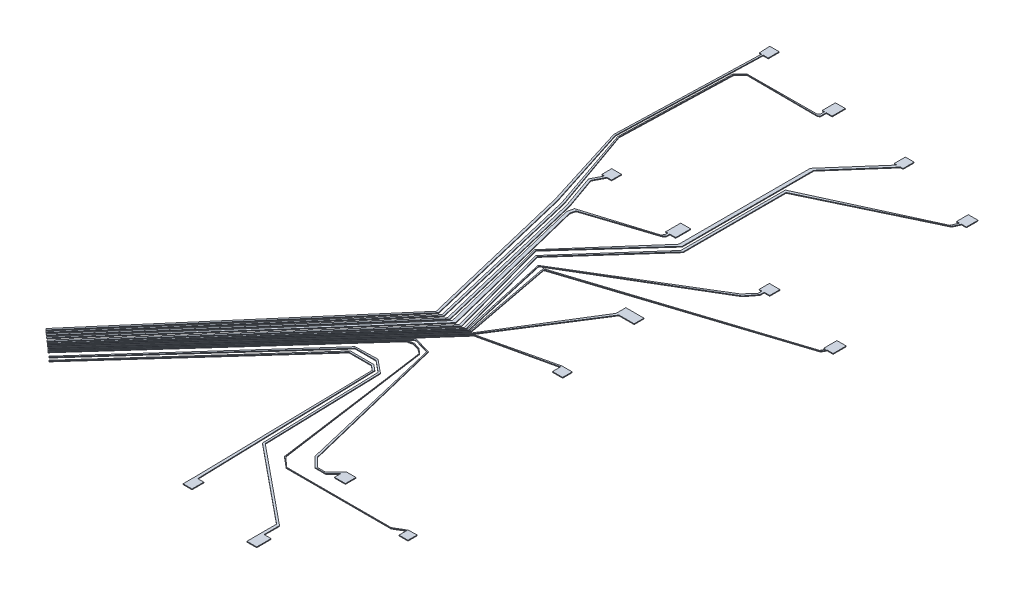
SolidWorks part; units mm, degrees
ref_plane "Front Plane" through (0, 0, 0) normal (0, 0, 1) x (1, 0, 0)
ref_plane "Top Plane" through (0, 0, 0) normal (0, 1, 0) x (1, 0, 0)
ref_plane "Right Plane" through (0, 0, 0) normal (1, 0, 0) x (0, 0, -1)
sketch "Sketch3" plane through (0, 0, 0) normal (0, 1, 0) x (1, 0, 0)
  line L0 (-35.1041, -266.8621) -> (862.8959, -266.8621) construction
  line L1 (-38.0962, 94.7327) -> (-39.2981, 55.2572)
  line L2 (-39.2981, 55.2572) -> (-31.9561, 31.8665)
  line L3 (-31.9561, 31.8665) -> (-21.5828, -11.2878)
  line L4 (-21.5828, -11.2878) -> (-71.1597, -69.0968)
  line L5 (-71.1597, -69.0968) -> (-70.7842, -69.4189)
  line L6 (-70.7842, -69.4189) -> (-20.9311, -11.2878)
  line L7 (-20.9311, -11.2878) -> (-31.3218, 31.8665)
  line L8 (-31.3218, 31.8665) -> (-38.8599, 55.2572)
  line L9 (-38.8599, 55.2572) -> (-37.658, 94.7327)
  line L10 (-37.658, 94.7327) -> (-36.253, 94.7327)
  line L11 (-36.253, 94.7327) -> (-36.253, 97.745)
  line L12 (-36.253, 97.745) -> (-38.8599, 97.745)
  line L13 (-38.8599, 97.745) -> (-38.6971, 94.7327)
  line L14 (-38.6971, 94.7327) -> (-38.0962, 94.7327)
  line L15 (-15.7108, 89.6823) -> (-15.7108, 88.591)
  line L17 (-35.4155, 88.0044) -> (-37.2858, 86.1341)
  line L18 (-37.2858, 86.1341) -> (-38.2259, 55.2572)
  line L19 (-38.2259, 55.2572) -> (-30.2079, 31.8665)
  line L20 (-30.2079, 31.8665) -> (-19.9928, -11.2878)
  line L21 (-19.9928, -11.2878) -> (-70.5361, -69.6927)
  line L22 (-70.5361, -69.6927) -> (-70.2221, -69.9644)
  line L23 (-70.2221, -69.9644) -> (-19.4438, -11.2878)
  line L24 (-19.4438, -11.2878) -> (-29.7, 32.0406)
  line L25 (-29.7, 32.0406) -> (-37.9562, 55.3497)
  line L26 (-37.9562, 55.3497) -> (-37.0216, 86.0456)
  line L27 (-37.0216, 86.0456) -> (-35.2614, 87.8504)
  line L28 (-35.2614, 87.8504) -> (-15.7108, 87.7531)
  line L29 (-15.7108, 87.7531) -> (-15.2357, 88.1064)
  line L30 (-15.2357, 88.1064) -> (-15.2357, 89.6823)
  line L31 (-15.2357, 89.6823) -> (-13.6188, 89.6823)
  line L32 (-13.6188, 89.6823) -> (-13.6188, 93.3116)
  line L33 (-13.6188, 93.3116) -> (-16.325, 93.3116)
  line L34 (-16.325, 93.3116) -> (-16.325, 89.6823)
  line L35 (-16.325, 89.6823) -> (-15.7108, 89.6823)
  line L36 (-15.7108, 88.591) -> (-16.1954, 88.1064)
  line L37 (-16.1954, 88.1064) -> (-35.4155, 88.0044)
  line L38 (-30.6711, 44.1014) -> (-32.1687, 41.1714)
  line L39 (-32.1687, 41.1714) -> (-28.9456, 32.0406)
  line L40 (-28.9456, 32.0406) -> (-18.4952, -11.2878)
  line L41 (-18.4952, -11.2878) -> (-69.8872, -70.3011)
  line L42 (-69.8872, -70.3011) -> (-69.5247, -70.6168)
  line L43 (-69.5247, -70.6168) -> (-17.8577, -11.2878)
  line L44 (-17.8577, -11.2878) -> (-28.3432, 32.1859)
  line L45 (-28.3432, 32.1859) -> (-31.515, 41.1714)
  line L46 (-31.515, 41.1714) -> (-30.0174, 44.1014)
  line L47 (-30.0174, 44.1014) -> (-28.7234, 44.1014)
  line L48 (-28.7234, 44.1014) -> (-28.7234, 46.8397)
  line L49 (-28.7234, 46.8397) -> (-31.4199, 46.8397)
  line L50 (-31.4199, 46.8397) -> (-31.4199, 44.1014)
  line L51 (-31.4199, 44.1014) -> (-30.6711, 44.1014)
  line L52 (-8.3665, 39.2375) -> (-8.3665, 38.4261)
  line L53 (-8.3665, 38.4261) -> (-8.9614, 37.743)
  line L54 (-8.9614, 37.743) -> (-27.0118, 32.1859)
  line L55 (-27.0118, 32.1859) -> (-27.41, 30.4396)
  line L56 (-27.41, 30.4396) -> (-17.1484, -11.2878)
  line L57 (-17.1484, -11.2878) -> (-69.1213, -70.9681)
  line L58 (-69.1213, -70.9681) -> (-68.8091, -71.24)
  line L59 (-68.8091, -71.24) -> (-16.1954, -11.2878)
  line L60 (-16.1954, -11.2878) -> (-26.6101, 30.4396)
  line L61 (-26.6101, 30.4396) -> (-26.2847, 31.8665)
  line L62 (-26.2847, 31.8665) -> (-8.3665, 37.743)
  line L63 (-8.3665, 37.743) -> (-7.8273, 38.3575)
  line L64 (-7.8273, 38.3575) -> (-7.8273, 39.2375)
  line L65 (-7.8273, 39.2375) -> (-6.2056, 39.2375)
  line L66 (-6.2056, 39.2375) -> (-6.2056, 43.3527)
  line L67 (-6.2056, 43.3527) -> (-8.9614, 43.3527)
  line L68 (-8.9614, 43.3527) -> (-8.9614, 39.2375)
  line L69 (-8.9614, 39.2375) -> (-8.3665, 39.2375)
  line L70 (6.9786, 86.9535) -> (-4.1836, 74.2344)
  line L71 (-4.1836, 74.2344) -> (-4.1836, 38.0503)
  line L72 (-4.1836, 38.0503) -> (-22.7104, 16.9395)
  line L73 (-22.7104, 16.9395) -> (-15.2357, -11.2878)
  line L74 (-15.2357, -11.2878) -> (-68.267, -71.7157)
  line L75 (-68.267, -71.7157) -> (-67.9028, -72.0353)
  line L76 (-67.9028, -72.0353) -> (-14.5911, -11.2878)
  line L77 (-14.5911, -11.2878) -> (-22.3907, 16.9395)
  line L78 (-22.3907, 16.9395) -> (-3.2205, 38.0503)
  line L79 (-3.2205, 38.0503) -> (-3.2205, 74.2344)
  line L80 (-3.2205, 74.2344) -> (7.9417, 86.9535)
  line L81 (7.9417, 86.9535) -> (8.6346, 86.9535)
  line L82 (8.6346, 86.9535) -> (8.6346, 90.0049)
  line L83 (8.6346, 90.0049) -> (6.2136, 90.0049)
  line L84 (6.2136, 90.0049) -> (6.2136, 86.9535)
  line L85 (6.2136, 86.9535) -> (6.9786, 86.9535)
  line L86 (29.4131, 81.7337) -> (28.6128, 81.7337)
  line L87 (28.6128, 81.7337) -> (28.6128, 84.935)
  line L88 (28.6128, 84.935) -> (31.2759, 84.935)
  line L89 (31.2759, 84.935) -> (31.2759, 81.7337)
  line L90 (31.2759, 81.7337) -> (29.9443, 81.7337)
  line L91 (29.4131, 81.7337) -> (28.6128, 79.8607)
  line L92 (28.6128, 79.8607) -> (-2.432, 65.6299)
  line L93 (-2.432, 65.6299) -> (-2.432, 36.8539)
  line L94 (-2.432, 36.8539) -> (-21.1993, 15.6499)
  line L95 (-21.1993, 15.6499) -> (-13.8535, -11.2878)
  line L96 (-13.8535, -11.2878) -> (-67.7398, -72.1703)
  line L97 (-67.7398, -72.1703) -> (-67.4613, -72.4168)
  line L98 (-67.4613, -72.4168) -> (-13.3568, -11.2878)
  line L99 (-13.3568, -11.2878) -> (-20.7026, 15.6499)
  line L100 (-20.7026, 15.6499) -> (-1.7624, 36.8539)
  line L101 (-1.7624, 36.8539) -> (-1.7624, 65.1584)
  line L102 (-1.7624, 65.1584) -> (29.1038, 79.8607)
  line L103 (29.1038, 79.8607) -> (29.9443, 81.7337)
  line L104 (18.4293, 38.3575) -> (18.4293, 37.2589)
  line L105 (18.4293, 37.2589) -> (16.0951, 34.6456)
  line L106 (16.0951, 34.6456) -> (-18.4952, 13.6781)
  line L107 (-18.4952, 13.6781) -> (-13.0522, -11.2878)
  line L108 (-13.0522, -11.2878) -> (-67.3236, -72.5386)
  line L109 (-67.3236, -72.5386) -> (-67.1813, -72.6647)
  line L110 (-67.1813, -72.6647) -> (-12.6528, -11.2878)
  line L111 (-12.6528, -11.2878) -> (-18.2652, 13.607)
  line L112 (-18.2652, 13.607) -> (16.8664, 34.4724)
  line L113 (16.8664, 34.4724) -> (19.0123, 37.2589)
  line L114 (19.0123, 37.2589) -> (19.0123, 38.3575)
  line L115 (19.0123, 38.3575) -> (20.5371, 38.3575)
  line L116 (20.5371, 38.3575) -> (20.5371, 41.1714)
  line L117 (20.5371, 41.1714) -> (17.6287, 41.1714)
  line L118 (17.6287, 41.1714) -> (17.6287, 38.3575)
  line L119 (17.6287, 38.3575) -> (18.4293, 38.3575)
  line L120 (41.0327, 33.2477) -> (40.5426, 32.1555)
  line L121 (40.5426, 32.1555) -> (-17.0297, 13.607)
  line L122 (-17.0297, 13.607) -> (-12.2554, -11.2878)
  line L123 (-12.2554, -11.2878) -> (-66.9593, -72.862)
  line L124 (-66.9593, -72.862) -> (-66.7471, -73.0505)
  line L125 (-66.7471, -73.0505) -> (-11.9371, -11.3568)
  line L126 (-11.9371, -11.3568) -> (-16.6818, 13.3837)
  line L127 (-16.6818, 13.3837) -> (40.7986, 32.0406)
  line L128 (40.7986, 32.0406) -> (41.4867, 33.2477)
  line L129 (41.4867, 33.2477) -> (43.0955, 33.2477)
  line L130 (43.0955, 33.2477) -> (43.0955, 36.8539)
  line L131 (43.0955, 36.8539) -> (40.5426, 36.8539)
  line L132 (40.5426, 36.8539) -> (40.5426, 33.2477)
  line L133 (40.5426, 33.2477) -> (41.0327, 33.2477)
  line L134 (3.6561, 15.6499) -> (3.6561, 12.9528)
  line L135 (3.6561, 12.9528) -> (-11.3992, -11.3568)
  line L136 (-11.3992, -11.3568) -> (-66.4465, -73.3175)
  line L137 (-66.4465, -73.3175) -> (-66.1994, -73.5371)
  line L138 (-66.1994, -73.5371) -> (-11.1522, -11.5763)
  line L139 (-11.1522, -11.5763) -> (4.4481, 12.9528)
  line L140 (4.4481, 12.9528) -> (8.6346, 12.9528)
  line L141 (8.6346, 12.9528) -> (8.6346, 15.6499)
  line L142 (8.6346, 15.6499) -> (3.6561, 15.6499)
  line L143 (8.7822, -7.029) -> (11.5694, -7.029)
  line L144 (11.5694, -7.029) -> (11.5694, -9.656)
  line L145 (11.5694, -9.656) -> (8.7822, -9.656)
  line L146 (8.7822, -7.029) -> (-10.8736, -11.6421)
  line L147 (-10.8736, -11.6421) -> (-66.0079, -73.7101)
  line L148 (-66.0079, -73.7101) -> (-65.8061, -73.8894)
  line L149 (-65.8061, -73.8894) -> (-10.6718, -11.8213)
  line L150 (-10.6718, -11.8213) -> (8.7822, -7.4371)
  line L151 (8.7822, -7.4371) -> (8.7822, -9.656)
  line L152 (4.4481, -61.9395) -> (1.5388, -64.8488)
  line L153 (1.5388, -64.8488) -> (-0.7647, -64.8488)
  line L154 (-0.7647, -64.8488) -> (-3.1784, -62.435)
  line L155 (-3.1784, -62.435) -> (-13.0522, -22.0112)
  line L156 (-13.0522, -22.0112) -> (-17.8577, -20.6062)
  line L157 (-17.8577, -20.6062) -> (-65.6933, -73.9936)
  line L158 (-65.6933, -73.9936) -> (-65.5794, -74.0956)
  line L159 (-65.5794, -74.0956) -> (-17.9394, -21.1942)
  line L160 (-17.9394, -21.1942) -> (-17.4934, -20.9326)
  line L161 (-17.4934, -20.9326) -> (-13.462, -22.1113)
  line L162 (-13.462, -22.1113) -> (-13.215, -22.3337)
  line L163 (-13.215, -22.3337) -> (-3.7017, -62.5628)
  line L164 (-3.7017, -62.5628) -> (-1.0902, -65.1743)
  line L165 (-1.0902, -65.1743) -> (1.8643, -65.1743)
  line L166 (1.8643, -65.1743) -> (3.9788, -63.0598)
  line L167 (3.9788, -63.0598) -> (3.9788, -64.8488)
  line L168 (3.9788, -64.8488) -> (6.9786, -64.8488)
  line L169 (6.9786, -64.8488) -> (6.9786, -61.9395)
  line L170 (6.9786, -61.9395) -> (4.4481, -61.9395)
  line L171 (26.7555, -67.2967) -> (23.7698, -69.0477)
  line L172 (23.7698, -69.0477) -> (-4.9637, -69.0477)
  line L173 (-4.9637, -69.0477) -> (-7.7118, -66.5729)
  line L174 (-7.7118, -66.5729) -> (-13.7589, -23.7093)
  line L175 (-13.7589, -23.7093) -> (-15.139, -22.4664)
  line L176 (-15.139, -22.4664) -> (-17.0297, -21.9137)
  line L177 (-17.0297, -21.9137) -> (-18.7266, -22.3149)
  line L178 (-18.7266, -22.3149) -> (-65.4565, -74.2057)
  line L179 (-65.4565, -74.2057) -> (-65.2657, -74.3776)
  line L180 (-65.2657, -74.3776) -> (-18.676, -22.5292)
  line L181 (-18.676, -22.5292) -> (-17.0297, -22.1398)
  line L182 (-17.0297, -22.1398) -> (-15.1999, -22.6748)
  line L183 (-15.1999, -22.6748) -> (-13.8288, -23.7516)
  line L184 (-13.8288, -23.7516) -> (-7.8849, -66.5974)
  line L185 (-7.8849, -66.5974) -> (-7.8602, -66.7755)
  line L186 (-7.8602, -66.7755) -> (-4.9637, -69.1848)
  line L187 (-4.9637, -69.1848) -> (23.9108, -69.1848)
  line L188 (23.9108, -69.1848) -> (26.6447, -67.5814)
  line L189 (26.6447, -67.5814) -> (26.6447, -69.7531)
  line L190 (26.6447, -69.7531) -> (29.1038, -69.7531)
  line L191 (29.1038, -69.7531) -> (29.1038, -67.23)
  line L192 (29.1038, -67.23) -> (26.7555, -67.2967)
  line L193 (-14.5144, -83.987) -> (-15.9393, -33.8333)
  line L194 (-15.9393, -33.8333) -> (-17.4649, -32.5643)
  line L195 (-17.4649, -32.5643) -> (-23.9346, -32.5643)
  line L196 (-23.9346, -32.5643) -> (-63.1861, -76.2463)
  line L197 (-63.1861, -76.2463) -> (-62.9836, -76.4283)
  line L198 (-62.9836, -76.4283) -> (-23.8373, -33.0265)
  line L199 (-23.8373, -33.0265) -> (-17.6727, -33.0265)
  line L200 (-17.6727, -33.0265) -> (-16.3054, -34.1638)
  line L201 (-16.3054, -34.1638) -> (-15.3112, -83.5011)
  line L202 (-15.3112, -83.5011) -> (-15.3112, -87.2364)
  line L203 (-15.3112, -87.2364) -> (-12.8374, -87.2364)
  line L204 (-12.8374, -87.2364) -> (-12.8374, -83.987)
  line L205 (-12.8374, -83.987) -> (-14.5144, -83.987)
  line L206 (7.184, -88.1861) -> (7.184, -83.987)
  line L207 (7.184, -83.987) -> (-14.0866, -66.5974)
  line L208 (-14.0866, -66.5974) -> (-15.0175, -33.8333)
  line L209 (-15.0175, -33.8333) -> (-18.1721, -31.2543)
  line L210 (-18.1721, -31.2543) -> (-23.9346, -31.2543)
  line L211 (-23.9346, -31.2543) -> (-63.919, -75.5146)
  line L212 (-63.919, -75.5146) -> (-64.1651, -75.2922)
  line L213 (-64.1651, -75.2922) -> (-24.3212, -30.905)
  line L214 (-24.3212, -30.905) -> (-18.1721, -30.7303)
  line L215 (-18.1721, -30.7303) -> (-14.5144, -33.7206)
  line L216 (-14.5144, -33.7206) -> (-13.5876, -66.3417)
  line L217 (-13.5876, -66.3417) -> (7.9417, -83.9429)
  line L218 (7.9417, -83.9429) -> (7.9417, -88.1861)
  line L219 (7.9417, -88.1861) -> (9.8765, -88.1861)
  line L220 (9.8765, -88.1861) -> (9.8765, -92.1635)
  line L221 (9.8765, -92.1635) -> (7.184, -92.1635)
  line L222 (7.184, -92.1635) -> (7.184, -88.1861)
  point P0 (3.2167, 6.8494)
extrude "Boss-Extrude1" add sketch "Sketch3" along normal blind 0.2
